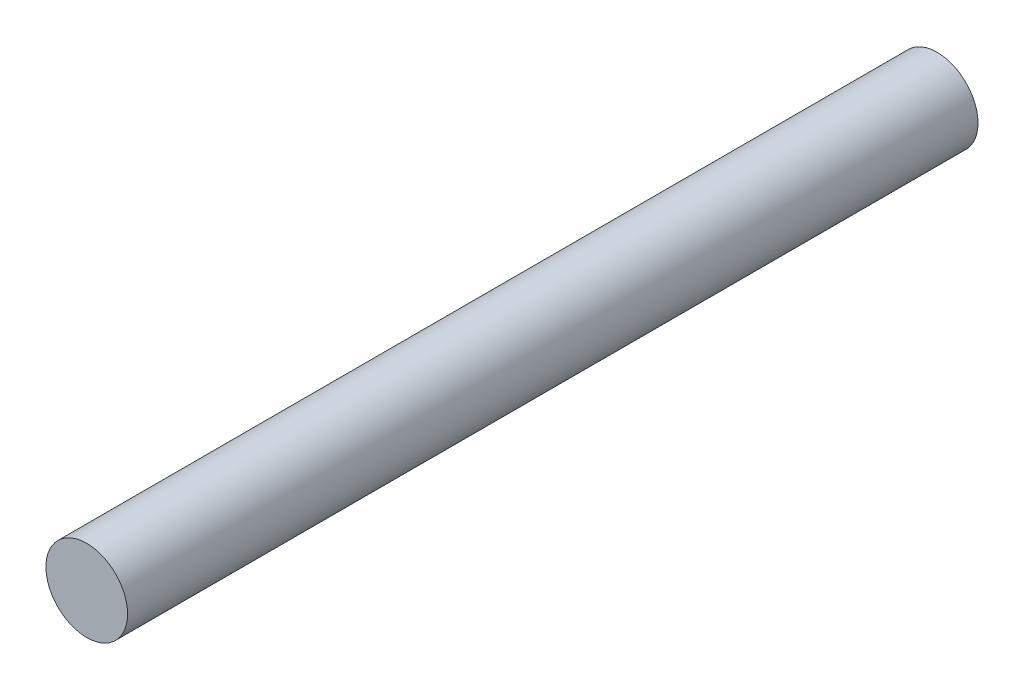
SolidWorks part; units mm, degrees
ref_plane "Front Plane" through (0, 0, 0) normal (0, 0, 1) x (1, 0, 0)
ref_plane "Top Plane" through (0, 0, 0) normal (0, 1, 0) x (1, 0, 0)
ref_plane "Right Plane" through (0, 0, 0) normal (1, 0, 0) x (0, 0, -1)
sketch "Sketch2" plane through (0, 0, 0) normal (0, 0, 1) x (1, 0, 0)
  circle A0 centre (0, 0) radius 6
  dimension "D1" = 12
extrude "Boss-Extrude1" add sketch "Sketch2" along normal blind 125
